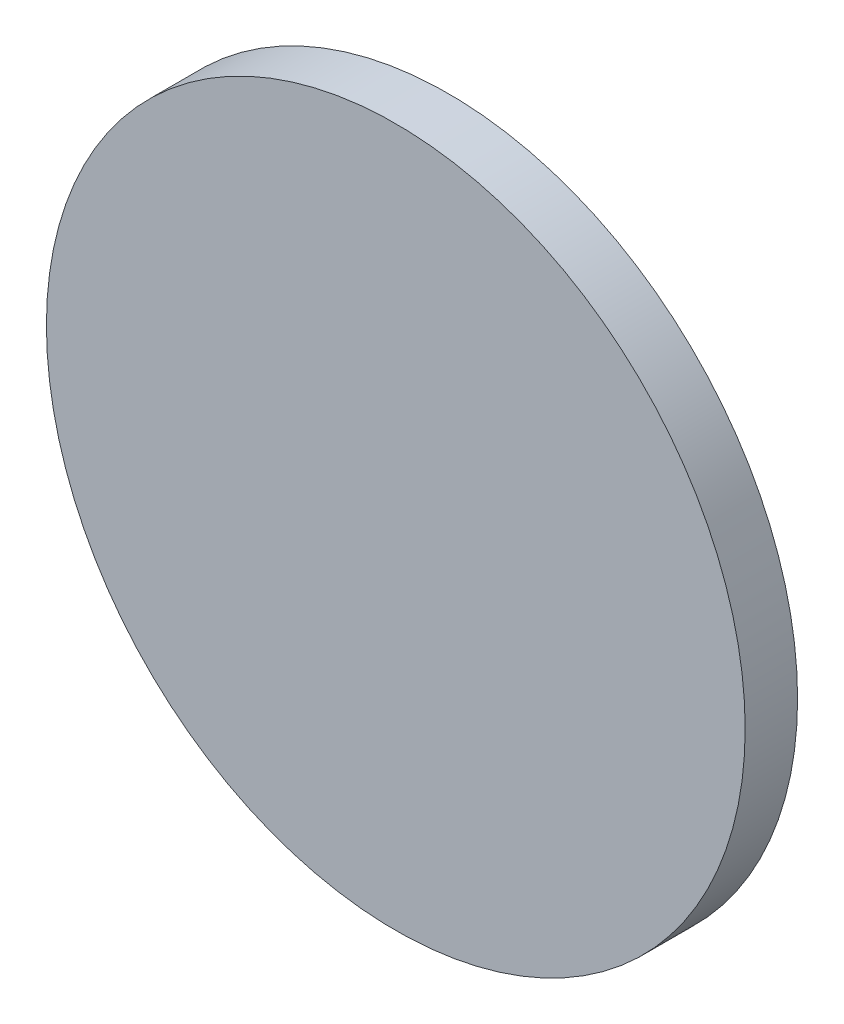
SolidWorks part; units mm, degrees
ref_plane "Front Plane" through (0, 0, 0) normal (0, 0, 1) x (1, 0, 0)
ref_plane "Top Plane" through (0, 0, 0) normal (0, 1, 0) x (1, 0, 0)
ref_plane "Right Plane" through (0, 0, 0) normal (1, 0, 0) x (0, 0, -1)
sketch "Sketch1" plane through (0, 0, 0) normal (0, 0, 1) x (1, 0, 0)
  circle A0 centre (0, 0) radius 20
  point P4 (0, 0)
  dimension "D1" = 40
extrude "Boss-Extrude1" add sketch "Sketch1" along normal blind 3
